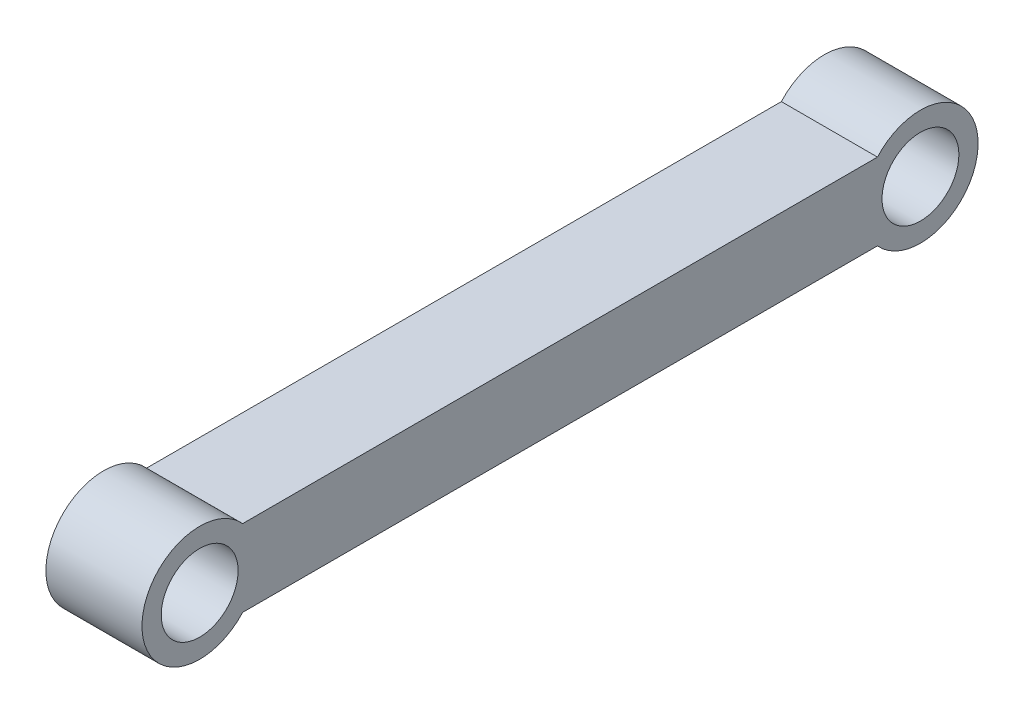
SolidWorks part; units mm, degrees
material "Thornel Mat VMA Custom"
ref_plane "Front Plane" through (0, 0, 0) normal (0, 0, 1) x (1, 0, 0)
ref_plane "Top Plane" through (0, 0, 0) normal (0, 1, 0) x (1, 0, 0)
ref_plane "Right Plane" through (0, 0, 0) normal (1, 0, 0) x (0, 0, -1)
sketch "LinkFrame" plane through (0, 0, 0) normal (1, 0, 0) x (0, 0, -1)
  line L0 (-490.3455, -226.2633) -> (259.6545, -226.2633) construction
  line L1 (-445.6242, -186.2633) -> (214.9331, -186.2633)
  line L2 (-445.6242, -266.2633) -> (214.9331, -266.2633)
  arc A1 (214.9331, -266.2633) -> (214.9331, -186.2633) centre (259.6545, -226.2633) ccw
  arc A2 (-445.6242, -186.2633) -> (-445.6242, -266.2633) centre (-490.3455, -226.2633) ccw
  circle A5 centre (-490.3455, -226.2633) radius 40
  circle A6 centre (259.6545, -226.2633) radius 40
  dimension "D1" = 120
  dimension "D2" = 120
  dimension "D5" = 80
  dimension "D6" = 80
  dimension "D3" = 750
  dimension "D4" = 80
  dimension "D7" = 44.7214
  dimension "D8" = 44.7214
extrude "Boss-Extrude1" add sketch "LinkFrame" along normal blind 100
equation "\"D1@LinkFrame\" = 1.5 * \"HoleMountDiameter@PrintingPress.Assembly\""
equation "\"D2@LinkFrame\" = 1.5 * \"HoleMountDiameter@PrintingPress.Assembly\""
equation "\"LinkLength\"= 75cm"
equation "\"D3@LinkFrame\" = \"LinkLength\""
equation "\"D4@LinkFrame\" = \"HoleMountDiameter@PrintingPress.Assembly\""
equation "\"D5@LinkFrame\"=\"HoleMountDiameter@PrintingPress.Assembly\""
equation "\"D6@LinkFrame\"=\"HoleMountDiameter@PrintingPress.Assembly\""
equation "\"D1@Boss-Extrude1\"=\"RivetLength@PrintingPress.Assembly\""
